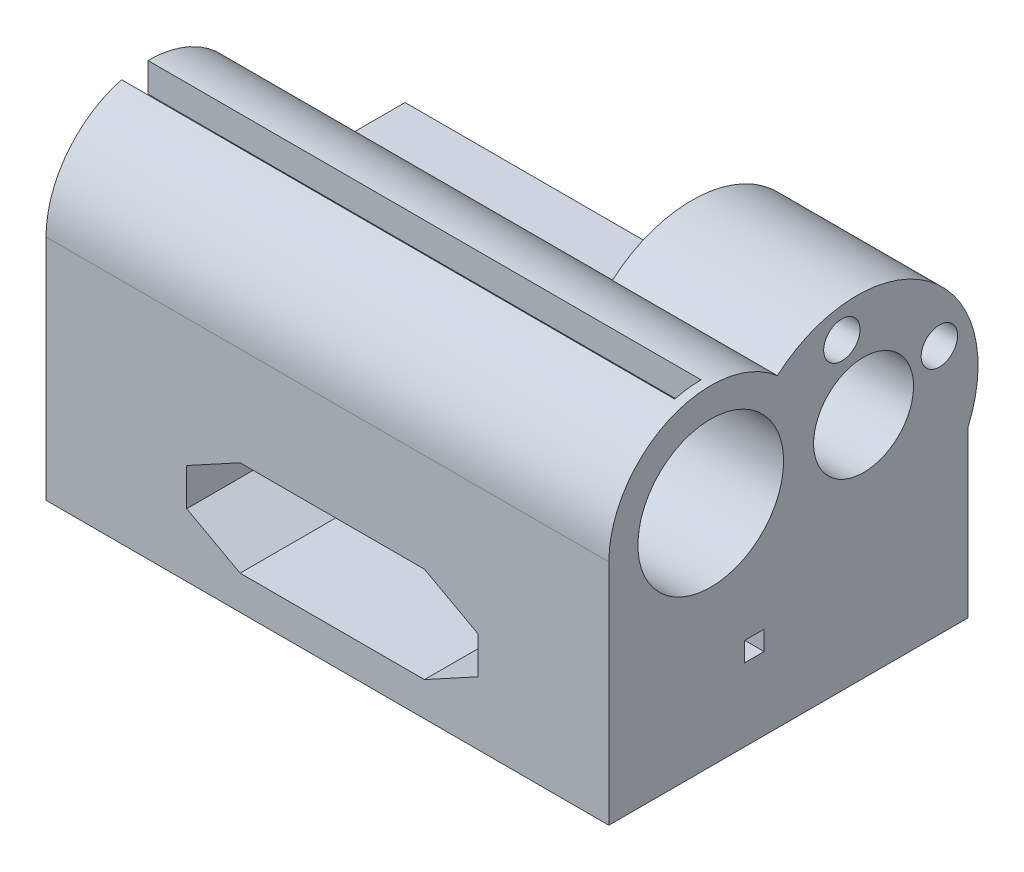
SolidWorks part; units mm, degrees
ref_plane "Front Plane" through (0, 0, 0) normal (0, 0, 1) x (1, 0, 0)
ref_plane "Top Plane" through (0, 0, 0) normal (0, 1, 0) x (1, 0, 0)
ref_plane "Right Plane" through (0, 0, 0) normal (1, 0, 0) x (0, 0, -1)
sketch "Sketch2" plane through (0, 0, 0) normal (0, 1, 0) x (1, 0, 0)
  line L1 (-29, -18.5) -> (29, -18.5)
  line L2 (-29, -18.5) -> (-29, 18.5)
  line L3 (-29, 18.5) -> (29, 18.5)
  line L4 (29, -18.5) -> (29, 18.5)
  line L5 (-29, -18.5) -> (29, 18.5) construction
  line L6 (-29, 18.5) -> (29, -18.5) construction
  point P0 (0, 0)
  dimension "D1" = 58
  dimension "D2" = 37
extrude "Boss-Extrude1" add sketch "Sketch2" along normal blind 17
sketch "Sketch3" plane through (29, 0, 0) normal (1, 0, 0) x (0, 0, -1)
  line L0 (-18.5, 0) -> (18.5, 0) construction
  line L1 (-18.5, 23.5) -> (-18.5, 17)
  line L2 (-18.5, 17) -> (-18.5, 0) construction
  line L5 (2.5, 23.5) -> (2.5, 17)
  line L6 (-18.5, 17) -> (18.5, 17) construction
  line L7 (-18.5, 17) -> (2.5, 17)
  arc A0 (2.5, 23.5) -> (-18.5, 23.5) centre (-8, 23.5) ccw
  dimension "D2" = 21
  dimension "D4" = 23.5
  dimension "D5" = 10.5
extrude "Boss-Extrude2" add sketch "Sketch3" against normal up to surface (58 mm away) up to face at (-29, 8.5, 0)
sketch "Sketch4" plane through (29, 0, 0) normal (1, 0, 0) x (0, 0, -1)
  line L1 (-18.5, 0) -> (18.5, 0) construction
  circle A0 centre (7.0436, 22) radius 12.5
  dimension "D1" = 25
  dimension "D2" = 22
extrude "Boss-Extrude3" add sketch "Sketch4" against normal blind 17
sketch "Sketch5" plane through (0, 0, -18.5) normal (0, 0, -1) x (-1, 0, 0)
  line L0 (-15.5, 6.5) -> (-15.5, 10.35)
  line L1 (-15.5, 10.35) -> (-10, 13.35)
  line L2 (-10, 13.35) -> (9, 13.35)
  line L3 (9, 13.35) -> (14.5, 10.357)
  line L4 (14.5, 10.357) -> (14.5, 6.5)
  line L5 (14.5, 6.5) -> (9, 3.5)
  line L6 (9, 3.5) -> (-10, 3.5)
  line L7 (-10, 3.5) -> (-15.5, 6.5)
  line L8 (-29, 0) -> (29, 0) construction
  line L9 (-29, 17) -> (-29, 0) construction
  line L10 (-23, 5.2045) -> (-23, 14.6536) construction
  line L11 (22, 4.2644) -> (22, 14.6536) construction
  line L12 (-23, 14.6536) -> (22, 14.6536) construction
  line L13 (-0.5, 14.6536) -> (-0.5, 7.909) construction
  line L14 (-29, 8.5) -> (29, 8.5) construction
  line L15 (29, 17) -> (29, 0) construction
  dimension "D1" = 3.85
  dimension "D2" = 3.857
  dimension "D3" = 3
  dimension "D4" = 3
  dimension "D5" = 5.5
  dimension "D6" = 5.5
  dimension "D8" = 5.5
  dimension "D9" = 19
  dimension "D10" = 3.5
  dimension "D11" = 15
  dimension "D12" = 6
  dimension "D13" = 45
extrude "Cut-Extrude1" cut sketch "Sketch5" against normal through all
sketch "Sketch6" plane through (0, 0, -18.5) normal (0, 0, -1) x (-1, 0, 0)
  line L0 (-29, 0) -> (29, 0) construction
  line L1 (-29, 17) -> (-29, 0) construction
  circle A0 centre (-23, 8.5) radius 4.076
  circle A1 centre (22, 8.5) radius 4.076
  dimension "D5" = 8.152
  dimension "D6" = 8.152
  dimension "D1" = 8.5
  dimension "D2" = 8.5
  dimension "D3" = 6
  dimension "D4" = 45
extrude "Cut-Extrude2" cut sketch "Sketch6" against normal blind 23
sketch "Sketch7" plane through (29, 0, 0) normal (1, 0, 0) x (0, 0, -1)
  line L0 (-18.5, 23.5) -> (-18.5, 0) construction
  line L1 (-18.5, 0) -> (18.5, 0) construction
  circle A0 centre (-8, 23.5) radius 7.5075
  circle A1 centre (7.7501, 23.5) radius 5.15
  dimension "D1" = 10.3
  dimension "D2" = 15.015
  dimension "D3" = 26.2501
  dimension "D4" = 23.5
extrude "Cut-Extrude3" cut sketch "Sketch7" against normal through all
sketch "Sketch8" plane through (29, 0, 0) normal (1, 0, 0) x (0, 0, -1)
  line L0 (7.7501, 23.5) -> (5.5097, 31.31) construction
  line L3 (7.7501, 23.5) -> (15.5601, 25.7405) construction
  line L4 (5.5097, 31.31) -> (6.0267, 29.5077) construction
  line L7 (15.5601, 25.7405) -> (13.7578, 25.2235) construction
  circle A1 centre (5.5097, 31.31) radius 1.875
  circle A2 centre (15.5601, 25.7405) radius 1.875
  dimension "D1" = 3.75
  dimension "D2" = 6.25
  dimension "D3" = 3.75
  dimension "D7" = 6.25
extrude "Cut-Extrude4" cut sketch "Sketch8" against normal through all
sketch "Sketch12" plane through (-29, 0, 0) normal (-1, 0, 0) x (0, 0, 1)
  line L0 (-18.5, 17) -> (-18.5, 0) construction
  line L1 (4.5, 7.5) -> (2.5, 7.5)
  line L2 (4.5, 7.5) -> (4.5, 9.5)
  line L3 (4.5, 9.5) -> (2.5, 9.5)
  line L4 (2.5, 7.5) -> (2.5, 9.5)
  line L5 (-18.5, 0) -> (18.5, 0) construction
  dimension "D1" = 23
  dimension "D2" = 2
  dimension "D3" = 2
  dimension "D4" = 7.5
extrude "Cut-Extrude6" cut sketch "Sketch12" against normal blind 8
mirror "Mirror1" about plane through (0, 0, 0) normal (1, 0, 0) of "Cut-Extrude6"
sketch "Sketch13" plane through (-29, 0, 0) normal (-1, 0, 0) x (0, 0, 1)
  line L0 (8, 23.5) -> (10.7176, 33.6422) construction
  line L1 (8, 23.5) -> (-2.5, 23.5) construction
  line L2 (8, 23.5) -> (8, 34) construction
  line L3 (9.9431, 30.7517) -> (10.7176, 33.6422)
  line L4 (8, 34) -> (8, 31.0075)
  arc A0 (9.9431, 30.7517) -> (8, 31.0075) centre (8, 23.5) ccw
  arc A1 (-2.5, 23.5) -> (8, 34) centre (8, 23.5) ccw
  arc A2 (18.5, 23.5) -> (-2.5, 23.5) centre (8, 23.5) ccw construction
  arc A3 (1.1397, 31.449) -> (-2.5, 23.5) centre (8, 23.5) ccw construction
  circle A4 centre (8, 23.5) radius 7.5075 construction
  circle M5 centre (8, 23.5) radius 7.5075
  arc M8 (18.5, 23.5) -> (-2.5, 23.5) centre (8, 23.5) ccw
  dimension "D1" = 15
  dimension "D2" = 90
extrude "Cut-Extrude7" cut sketch "Sketch13" against normal blind 57 contours L4 L3 M8 M5
sketch "Sketch14" plane through (0, 0, 0) normal (0, -1, 0) x (1, 0, 0)
  line L0 (0.5, -11.5) -> (29, -11.5) construction
  line L1 (29, 18.5) -> (29, -18.5) construction
  line L2 (0.5, -11.5) -> (0.5, -18.5) construction
  line L3 (29, -18.5) -> (-29, -18.5) construction
  circle A0 centre (0.5, -11.5) radius 1.5
  dimension "D1" = 3
  dimension "D2" = 7
  dimension "D3" = 28.5
extrude "Cut-Extrude8" cut sketch "Sketch14" against normal through all
